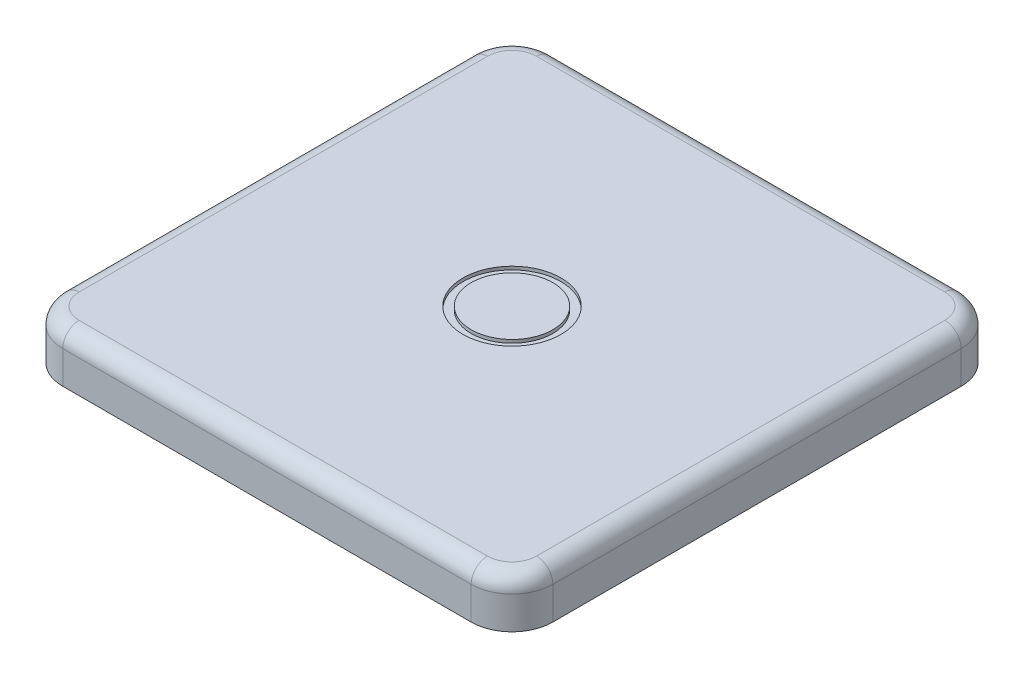
SolidWorks part; units mm, degrees
ref_plane "Front Plane" through (0, 0, 0) normal (0, 0, 1) x (1, 0, 0)
ref_plane "Top Plane" through (0, 0, 0) normal (0, 1, 0) x (1, 0, 0)
ref_plane "Right Plane" through (0, 0, 0) normal (1, 0, 0) x (0, 0, -1)
sketch "Sketch1" plane through (0, 0, 0) normal (0, 1, 0) x (1, 0, 0)
  line L1 (-15, 15) -> (15, 15)
  line L2 (-15, 15) -> (-15, -15)
  line L3 (-15, -15) -> (15, -15)
  line L4 (15, 15) -> (15, -15)
  line L5 (-15, 15) -> (15, -15) construction
  line L6 (-15, -15) -> (15, 15) construction
  point P0 (0, 0)
  dimension "D1" = 30
extrude "Boss-Extrude1" add sketch "Sketch1" along normal blind 3
fillet "Fillet1" radius 2.5 4 edges at (-15, 1.5, -15) (15, 1.5, -15) (-15, 1.5, 15) (15, 1.5, 15)
fillet "Fillet2" radius 1 8 edges at (14.2678, 3, -14.2678) (15, 3, 0) (14.2678, 3, 14.2678) (0, 3, 15) (-14.2678, 3, 14.2678) (-15, 3, 0) (-14.2678, 3, -14.2678) (0, 3, -15)
sketch "Sketch2" plane through (0, 3, 0) normal (0, 1, 0) x (1, 0, 0)
  circle A0 centre (0, 0) radius 2.5
  circle A1 centre (0, 0) radius 3
  dimension "D1" = 5
  dimension "D2" = 0.5
extrude "Cut-Extrude1" cut sketch "Sketch2" against normal blind 0.2 contours A1 A0
